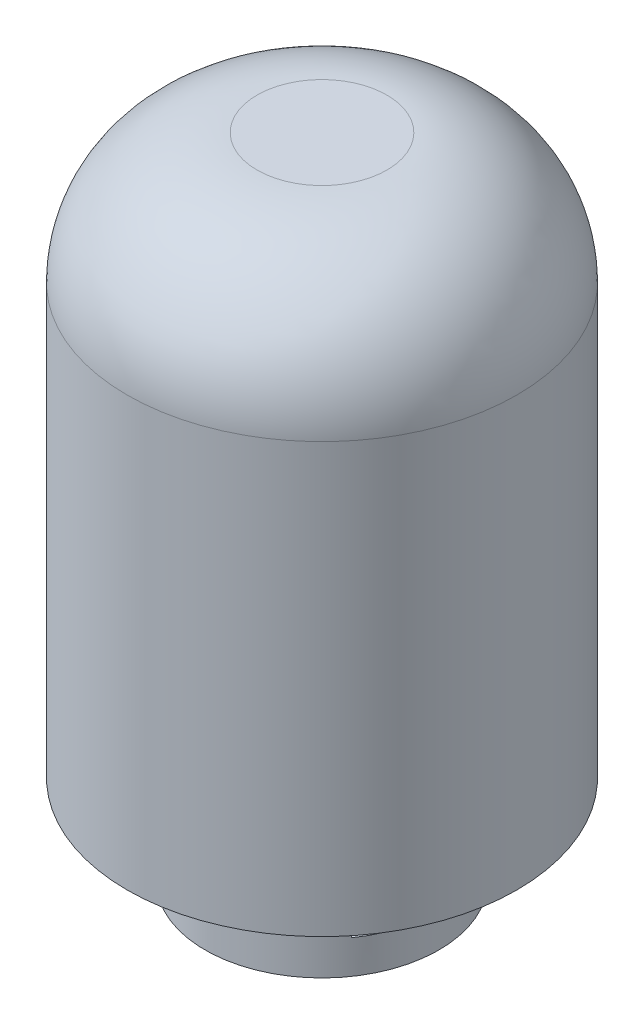
SolidWorks part; units mm, degrees
material "Ti-6Al-2Sn-2Zr-2Mo-2Cr-0.25Si (SS)"
ref_plane "Front Plane" through (0, 0, 0) normal (0, 0, 1) x (1, 0, 0)
ref_plane "Top Plane" through (0, 0, 0) normal (0, 1, 0) x (1, 0, 0)
ref_plane "Right Plane" through (0, 0, 0) normal (1, 0, 0) x (0, 0, -1)
sketch "Sketch1" plane through (0, 0, 0) normal (0, 1, 0) x (1, 0, 0)
  circle A0 centre (0, 0) radius 150
  dimension "D1" = 300
extrude "Boss-Extrude1" add sketch "Sketch1" along normal blind 500
sketch "Sketch2" plane through (0, 0, 0) normal (0, -1, 0) x (1, 0, 0)
  circle A0 centre (0, 0) radius 90
  circle A1 centre (0, 0) radius 150 construction
  circle A2 centre (0, 0) radius 150
  dimension "D1" = 60
extrude "Cut-Extrude1" cut sketch "Sketch2" against normal blind 70
sketch "Sketch3" plane through (0, 0, 0) normal (1, 0, 0) x (0, 0, -1)
  line L0 (0, 0) -> (0, 70) construction
  line L1 (-90, 70) -> (90, 70) construction
  line L3 (-51.2255, 44.1832) -> (51.2255, 44.1832)
  line L4 (-51.2255, 44.1832) -> (-51.2255, 25.8168)
  line L5 (-51.2255, 25.8168) -> (51.2255, 25.8168)
  line L6 (51.2255, 44.1832) -> (51.2255, 25.8168)
  line L7 (-51.2255, 44.1832) -> (51.2255, 25.8168) construction
  line L8 (-51.2255, 25.8168) -> (51.2255, 44.1832) construction
  point P5 (0, 35)
extrude "Cut-Extrude2" cut sketch "Sketch3" against normal through all both and the other way through all
fillet "Fillet1" radius 100 1 edges at (0, 500, 150)
sketch "Sketch4" plane through (0, 0, 0) normal (0, 0, 1) x (1, 0, 0)
  line L0 (0, 0) -> (0, 498.8605) construction
  circle A0 centre (0, 249.4303) radius 67.5
  dimension "D1" = 135
extrude "Cut-Extrude3" cut sketch "Sketch4" against normal through all
